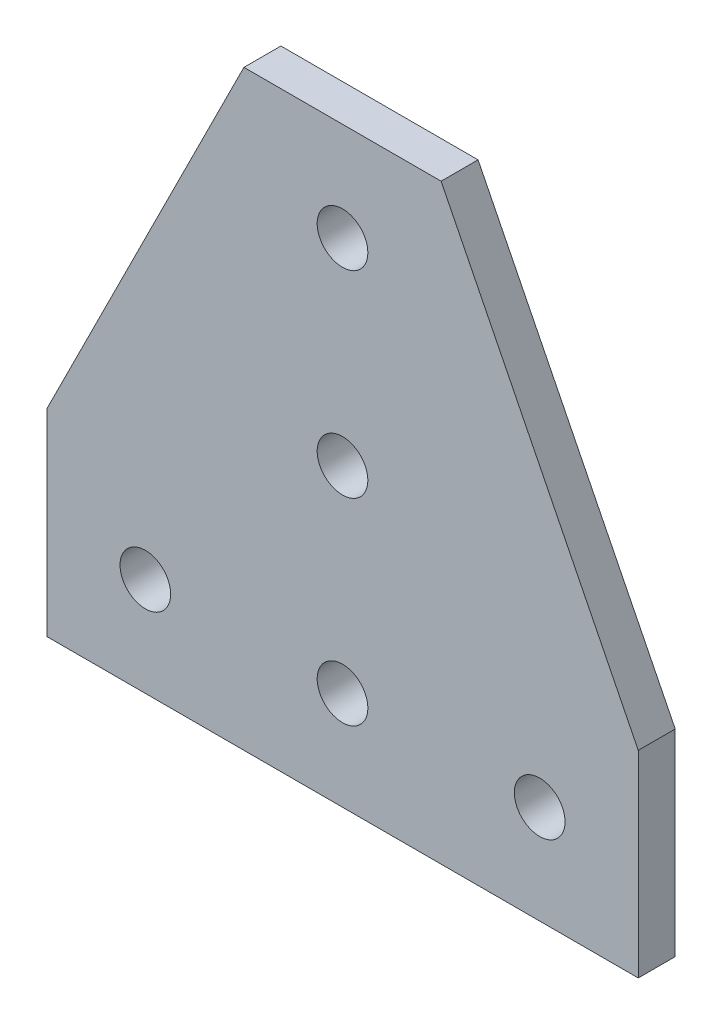
SolidWorks part; units mm, degrees
ref_plane "Front Plane" through (0, 0, 0) normal (0, 0, 1) x (1, 0, 0)
ref_plane "Top Plane" through (0, 0, 0) normal (0, 1, 0) x (1, 0, 0)
ref_plane "Right Plane" through (0, 0, 0) normal (1, 0, 0) x (0, 0, -1)
sketch "Sketch1" plane through (0, 0, 0) normal (0, 0, 1) x (1, 0, 0)
  line L0 (0, 0) -> (0, 25.4)
  line L1 (12.7, 12.7) -> (38.1, 12.7) construction
  line L2 (38.1, 12.7) -> (63.5, 12.7) construction
  line L3 (38.1, 63.5) -> (38.1, 76.2) construction
  line L4 (76.2, 25.4) -> (50.8, 76.2)
  line L5 (76.2, 0) -> (0, 0)
  line L6 (38.1, 38.1) -> (38.1, 63.5) construction
  line L7 (76.2, 25.4) -> (76.2, 0)
  line L8 (25.4, 76.2) -> (50.8, 76.2)
  line L9 (0, 25.4) -> (25.4, 76.2)
  line L11 (38.1, 12.7) -> (38.1, 38.1) construction
  circle A0 centre (12.7, 12.7) radius 3.2639
  circle A1 centre (38.1, 12.7) radius 3.2639
  circle A2 centre (63.5, 12.7) radius 3.2639
  circle A3 centre (38.1, 38.1) radius 3.2639
  circle A4 centre (38.1, 63.5) radius 3.2639
  dimension "D1" = 25.4
  dimension "E" = 6.5278
  dimension "D2" = 12.7
  dimension "D3" = 12.7
  dimension "B1" = 76.2
  dimension "C1" = 25.4
  dimension "C2" = 25.4
  dimension "B2" = 76.2
extrude "Boss-Extrude1" add sketch "Sketch1" along normal mid plane 4.7625
